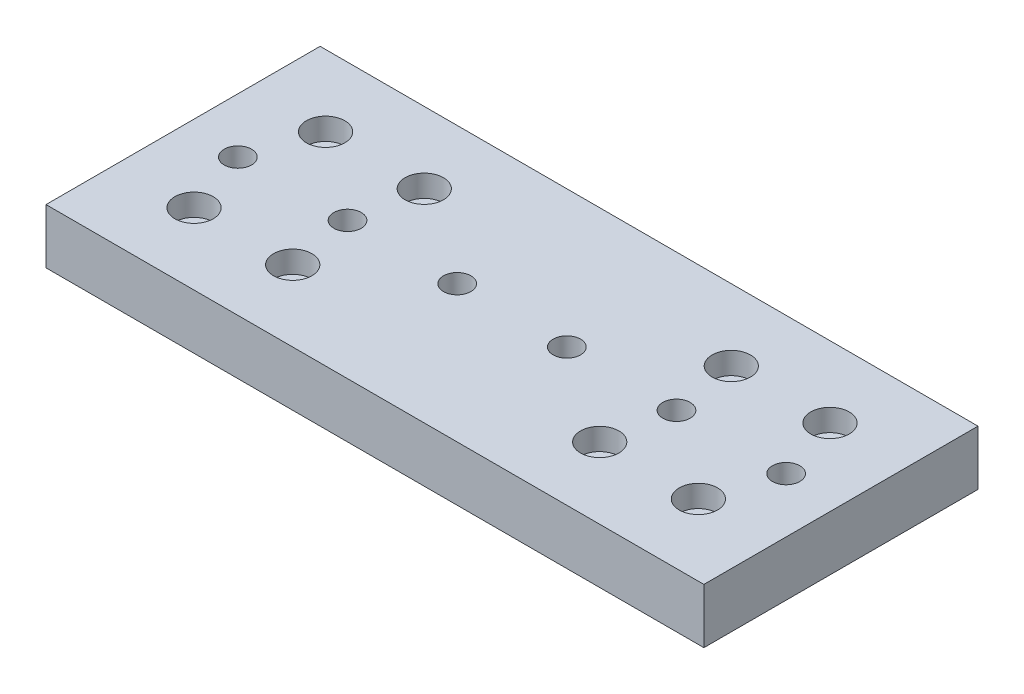
SolidWorks part; units mm, degrees
ref_plane "Front Plane" through (0, 0, 0) normal (0, 0, 1) x (1, 0, 0)
ref_plane "Top Plane" through (0, 0, 0) normal (0, 1, 0) x (1, 0, 0)
ref_plane "Right Plane" through (0, 0, 0) normal (1, 0, 0) x (0, 0, -1)
sketch "Sketch1" plane through (0, 0, 0) normal (0, 1, 0) x (1, 0, 0)
  line L1 (60, -25) -> (-60, -25)
  line L2 (60, -25) -> (60, 25)
  line L3 (60, 25) -> (-60, 25)
  line L4 (-60, -25) -> (-60, 25)
  line L5 (60, -25) -> (-60, 25) construction
  line L6 (60, 25) -> (-60, -25) construction
  point P0 (0, 0)
  dimension "D1" = 50
  dimension "D2" = 120
extrude "main" add sketch "Sketch1" along normal blind 10
sketch "Sketch2" plane through (0, 10, 0) normal (0, 1, 0) x (1, 0, 0)
  line L0 (-60, 0) -> (0, 0) construction
  line L1 (-60, 25) -> (-60, -25) construction
  line L2 (0, 0) -> (0, 25) construction
  line L3 (60, 25) -> (-60, 25) construction
  circle A0 centre (-28, -12) radius 1.5
  circle A1 centre (-46, -12) radius 1.5
  circle A3 centre (28, -12) radius 1.5
  circle A5 centre (46, -12) radius 1.5
  circle A7 centre (46, 12) radius 1.5
  circle A9 centre (28, 12) radius 1.5
  circle A12 centre (-46, 12) radius 1.5
  circle A16 centre (-28, 12) radius 1.5
  dimension "D1" = 3
  dimension "D2" = 24
  dimension "D3" = 18
  dimension "D4" = 14
extrude "linear_bearing_mount" cut sketch "Sketch2" against normal through all
sketch "Sketch5" plane through (0, 10, 0) normal (0, 1, 0) x (1, 0, 0)
  line L0 (0, 25) -> (0, 0) construction
  line L1 (60, 25) -> (-60, 25) construction
  line L2 (0, 0) -> (-60, 0) construction
  line L3 (-60, 25) -> (-60, -25) construction
  circle A0 centre (-46, 12) radius 3.5
  circle A1 centre (-28, 12) radius 3.5
  circle A2 centre (-28, -12) radius 3.5
  circle A3 centre (-46, -12) radius 3.5
  circle A4 centre (46, -12) radius 3.5
  circle A5 centre (28, -12) radius 3.5
  circle A6 centre (28, 12) radius 3.5
  circle A7 centre (46, 12) radius 3.5
  dimension "D1" = 7
extrude "linear_bearing_countersink" cut sketch "Sketch5" against normal blind 4
sketch "Sketch6" plane through (0, 0, 0) normal (0, -1, 0) x (1, 0, 0)
  line L0 (-60, 0) -> (60, 0) construction
  line L3 (-60, -25) -> (-60, 25) construction
  line L4 (60, 25) -> (60, -25) construction
  line L5 (-50, 0) -> (-30, 0) construction
  line L6 (0, 25) -> (0, -25) construction
  line L7 (-60, 25) -> (60, 25) construction
  line L8 (60, -25) -> (-60, -25) construction
  circle A4 centre (-50, 0) radius 2.5
  circle A5 centre (-30, 0) radius 2.5
  circle A6 centre (-10, 0) radius 2.5
  circle A7 centre (10, 0) radius 2.5
  circle A8 centre (30, 0) radius 2.5
  circle A9 centre (50, 0) radius 2.5
  dimension "D3" = 5
  dimension "D1" = 6
  dimension "D2" = 20
extrude "Cut-Extrude1" cut sketch "Sketch6" against normal through all
sketch "Sketch7" plane through (0, 0, 0) normal (0, -1, 0) x (1, 0, 0)
  circle A0 centre (-50, 0) radius 4.3
  circle A1 centre (-30, 0) radius 4.3
  circle A2 centre (-10, 0) radius 4.3
  circle A3 centre (10, 0) radius 4.3
  circle A4 centre (30, 0) radius 4.3
  circle A5 centre (50, 0) radius 4.3
  dimension "D1" = 8.6
extrude "Cut-Extrude2" cut sketch "Sketch7" against normal blind 5
